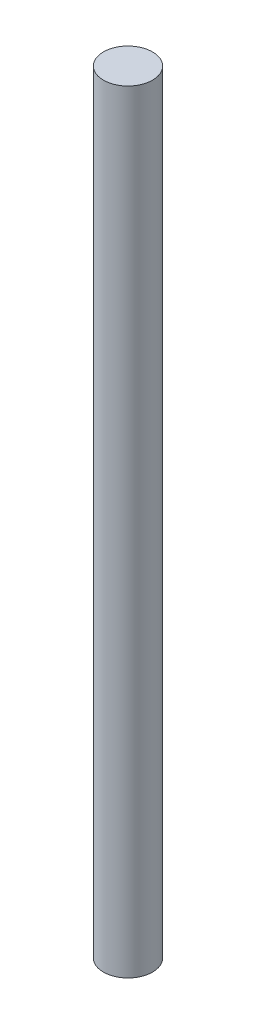
SolidWorks part; units mm, degrees
material "Acrylic (Medium-high impact)"
ref_plane "Front Plane" through (0, 0, 0) normal (0, 0, 1) x (1, 0, 0)
ref_plane "Top Plane" through (0, 0, 0) normal (0, 1, 0) x (1, 0, 0)
ref_plane "Right Plane" through (0, 0, 0) normal (1, 0, 0) x (0, 0, -1)
sketch "Sketch1" plane through (0, 0, 0) normal (0, 1, 0) x (1, 0, 0)
  circle A0 centre (0, 0) radius 6.35
  dimension "D1" = 12.7
extrude "Boss-Extrude1" add sketch "Sketch1" along normal blind 200.025
hole_wizard "#32 (0.116) Diameter Hole2" positions "Sketch4" profile "Sketch5" hole size "#32" standard "ANSI Inch"
sketch "Sketch4" plane through (0, 0, 0) normal (0, -1, 0) x (-1, 0, 0)
  point P0 (0, 0)
sketch "Sketch5" plane through (0, 0, 0) normal (1, 0, 0) x (0, 0, -1)
  line L0 (0, 0) -> (0, 4.5428)
  line L1 (0, 4.5428) -> (1.4732, 3.6576)
  line L2 (1.4732, 3.6576) -> (1.4732, 0)
  line L5 (1.4732, 0) -> (0, 0)
  line L10 (0, 4.5428) -> (-1.4732, 3.6576) construction
  line L11 (0, -6.35) -> (0, 107.95) construction
  dimension "Hole Dia." = 2.9464
  dimension "Hole Depth" = 3.6576
  dimension "Drill Angle" = 118
